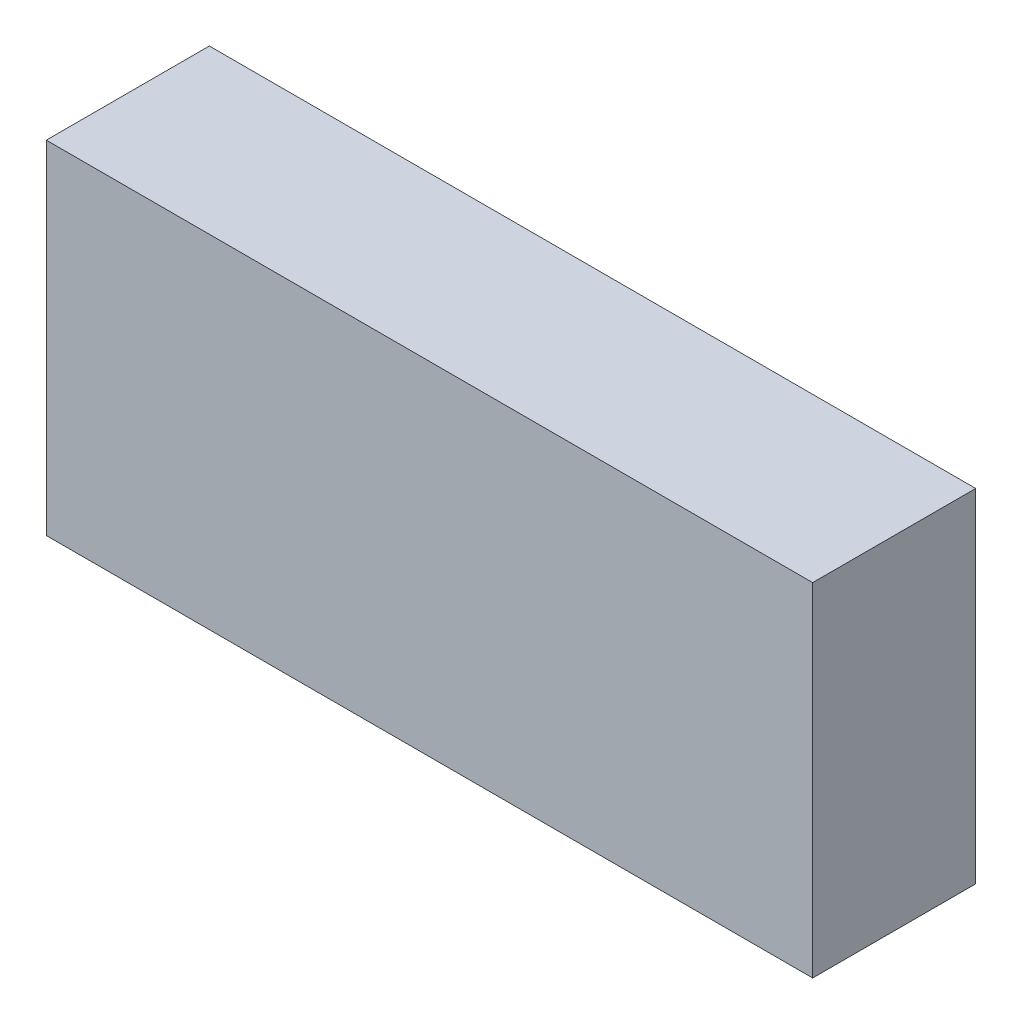
SolidWorks part; units mm, degrees
ref_plane "Front Plane" through (0, 0, 0) normal (0, 0, 1) x (1, 0, 0)
ref_plane "Top Plane" through (0, 0, 0) normal (0, 1, 0) x (1, 0, 0)
ref_plane "Right Plane" through (0, 0, 0) normal (1, 0, 0) x (0, 0, -1)
sketch "Sketch1" plane through (0, 0, 0) normal (0, 0, 1) x (1, 0, 0)
  line L1 (0, 0) -> (23.5, 0)
  line L2 (0, 0) -> (0, -10.5)
  line L3 (0, -10.5) -> (23.5, -10.5)
  line L4 (23.5, 0) -> (23.5, -10.5)
  dimension "D1" = 10.5
  dimension "D2" = 23.5
extrude "Boss-Extrude1" add sketch "Sketch1" along normal blind 5
